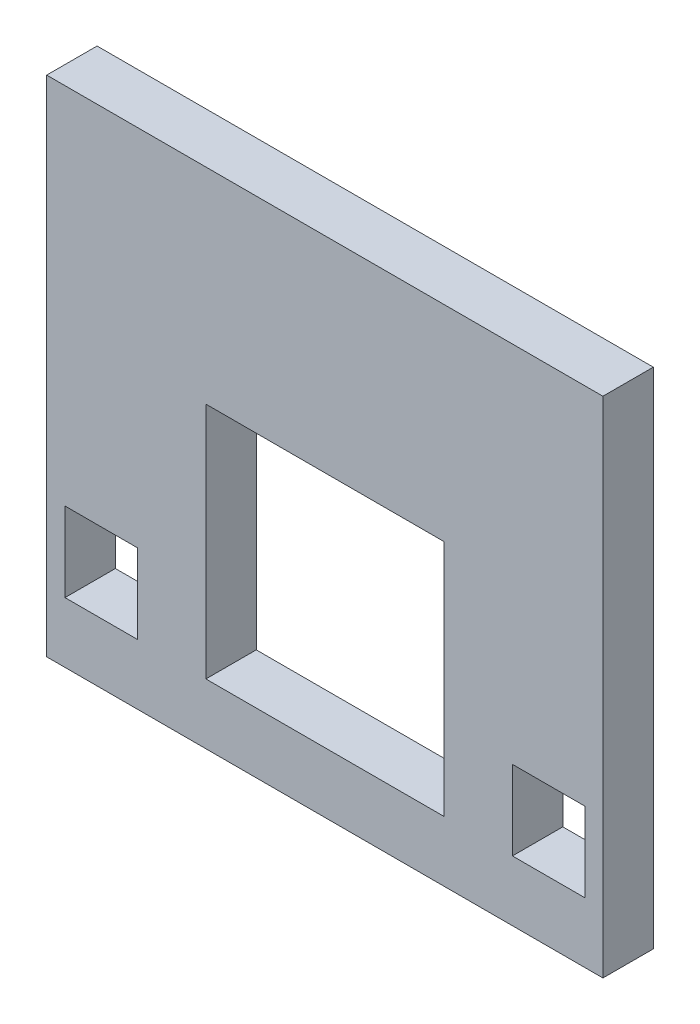
SolidWorks part; units mm, degrees
ref_plane "Front Plane" through (0, 0, 0) normal (0, 0, 1) x (1, 0, 0)
ref_plane "Top Plane" through (0, 0, 0) normal (0, 1, 0) x (1, 0, 0)
ref_plane "Right Plane" through (0, 0, 0) normal (1, 0, 0) x (0, 0, -1)
sketch "Sketch1" plane through (0, 0, 0) normal (0, 0, 1) x (1, 0, 0)
  line L1 (9.7704, 30.8752) -> (44.8224, 30.8752)
  line L2 (9.7704, 30.8752) -> (9.7704, -0.8748)
  line L3 (9.7704, -0.8748) -> (44.8224, -0.8748)
  line L4 (44.8224, 30.8752) -> (44.8224, -0.8748)
  dimension "D1" = 35.052
  dimension "D2" = 31.75
extrude "Boss-Extrude1" add sketch "Sketch1" along normal blind 3.175
sketch "Sketch2" plane through (0, 0, 3.175) normal (0, 0, 1) x (1, 0, 0)
  line L0 (10.9234, 19.4552) -> (43.6794, 19.4552) construction
  line L1 (10.9234, 19.4552) -> (10.9234, 9.1352) construction
  line L2 (43.6794, 19.4552) -> (43.6794, 9.1352) construction
  line L3 (19.8014, 9.4352) -> (19.8014, 17.9352) construction
  line L4 (19.8014, 17.9352) -> (34.8014, 17.9352) construction
  line L5 (34.8014, 17.9352) -> (34.8014, 9.1352) construction
  line L6 (10.9234, 9.1352) -> (10.9234, 7.9352) construction
  line L7 (10.9234, 7.9352) -> (15.4834, 7.9352) construction
  line L8 (19.8014, 8.2352) -> (19.8014, 9.4352) construction
  line L9 (43.6794, 9.1352) -> (43.6794, 7.9352) construction
  line L10 (43.6794, 7.9352) -> (39.1194, 7.9352) construction
  line L11 (34.8014, 7.9352) -> (34.8014, 9.1352) construction
  line L12 (15.4834, 7.9352) -> (15.4834, 2.9352) construction
  line L13 (15.4834, 2.9352) -> (19.8014, 2.9352) construction
  line L14 (19.8014, 2.9352) -> (19.8014, 8.2352) construction
  line L15 (34.8014, 7.9352) -> (34.8014, 2.9352) construction
  line L16 (34.8014, 2.9352) -> (38.1579, 2.9352) construction
  line L17 (39.1194, 7.9352) -> (39.1194, 2.9352) construction
  line L18 (39.1194, 2.9352) -> (38.1579, 2.9352) construction
  line L19 (9.7704, -0.8748) -> (44.8224, -0.8748) construction
  line L20 (19.8014, 17.9352) -> (34.8014, 17.9352)
  line L21 (19.8014, 17.9352) -> (19.8014, 2.9352)
  line L22 (19.8014, 2.9352) -> (34.8014, 2.9352)
  line L23 (34.8014, 17.9352) -> (34.8014, 2.9352)
  line L24 (39.1194, 7.9352) -> (43.6794, 7.9352)
  line L25 (39.1194, 7.9352) -> (39.1194, 2.9352)
  line L26 (39.1194, 2.9352) -> (43.6794, 2.9352)
  line L27 (43.6794, 7.9352) -> (43.6794, 2.9352)
  line L28 (10.9234, 7.9352) -> (15.4834, 7.9352)
  line L29 (10.9234, 7.9352) -> (10.9234, 2.9352)
  line L30 (10.9234, 2.9352) -> (15.4834, 2.9352)
  line L31 (15.4834, 7.9352) -> (15.4834, 2.9352)
  line L32 (44.8224, -0.8748) -> (44.8224, 30.8752) construction
  dimension "D1" = 3.81
  dimension "D2" = 15
  dimension "D3" = 15
  dimension "D4" = 5
  dimension "D5" = 5
  dimension "D6" = 4.56
  dimension "D7" = 4.56
  dimension "D8" = 4.318
  dimension "D9" = 4.318
  dimension "D10" = 1.143
extrude "Cut-Extrude1" cut sketch "Sketch2" against normal blind 3.175
